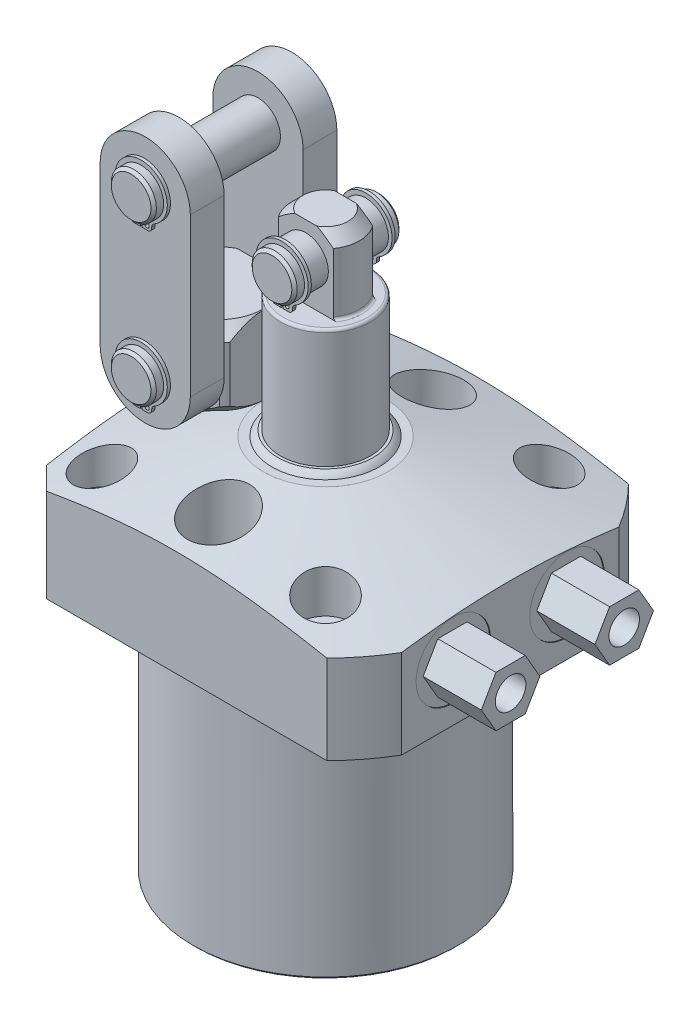
SolidWorks part; units mm, degrees
material "Alloy Steel"
ref_plane "Front Plane" through (0, 0, 0) normal (0, 0, 1) x (1, 0, 0)
ref_plane "Top Plane" through (0, 0, 0) normal (0, 1, 0) x (1, 0, 0)
ref_plane "Right Plane" through (0, 0, 0) normal (1, 0, 0) x (0, 0, -1)
sketch "Sketch28" plane through (0, 0, 0) normal (0, 0, 1) x (1, 0, 0)
  line L0 (0, 0) -> (0, 146.1857) construction
  line L1 (-17.4625, 36.4998) -> (-60.325, 25.0148)
  line L2 (-60.325, 25.0148) -> (-60.325, 0)
  line L3 (-60.325, 0) -> (-37.2999, 0)
  line L6 (-37.2999, 0) -> (-37.2999, -69.85)
  line L9 (-37.2999, -69.85) -> (0, -69.85)
  line L10 (0, -69.85) -> (0, 36.4998)
  line L11 (0, 36.4998) -> (-17.4625, 36.4998)
  dimension "D2" = 74.5998
  dimension "D3" = 69.85
  dimension "D5" = 120.65
  dimension "D6" = 15
  dimension "D7" = 34.925
  dimension "D8" = 36.4998
revolve "Revolve7" add sketch "Sketch28" angle 360 about L0
sketch "Sketch3" plane through (0, 36.4998, 0) normal (0, 1, 0) x (-1, 0, 0)
  line L0 (42.4688, -42.4688) -> (-51.9938, -42.4688)
  line L3 (-51.9938, 42.4688) -> (42.4688, 42.4688)
  line L4 (42.4688, -42.4688) -> (42.4688, 42.4688)
  line L5 (-51.9938, -42.4688) -> (-51.9938, 42.4688)
  line L6 (-29.7523, 0) -> (31.3525, 0) construction
  dimension "D1" = 84.9376
  dimension "D2" = 51.9938
  dimension "D5" = 42.4688
extrude "Cut-Extrude9" cut sketch "Sketch3" against normal up to next (106.3498 mm away) flip side to cut
chamfer "Chamfer8" distance 6.35 angle 45 2 edges at (-42.4688, 12.5429, -42.4688) (-42.4688, 12.5429, 42.4688)
chamfer "Chamfer5" distance 0.762 angle 45 1 edges at (0, -69.85, -37.2999)
hole_wizard "Hole1" positions "Sketch32" profile "Sketch31" legacy
sketch "Sketch32" plane through (0, 36.4998, 0) normal (0, 1, 0) x (-1, 0, 0)
  line L1 (0, 0) -> (-56.2722, 0) construction
  line L2 (0, 0) -> (0, 46.6984) construction
  point P11 (-31.496, -31.496)
  point P23 (-31.496, 31.496)
  point P25 (31.496, -31.496)
  point P26 (31.496, 31.496)
  dimension "D1" = 62.992
  dimension "D2" = 62.992
sketch "Sketch31" plane through (31.496, 36.4998, -31.496) normal (1, 0, 0) x (0, 0, 1)
  line L0 (0, 0) -> (0, 36.4998)
  line L1 (0, 36.4998) -> (4.3688, 36.4998)
  line L2 (4.3688, 36.4998) -> (4.3688, 17.4498)
  line L3 (4.3688, 17.4498) -> (7.1374, 17.4498)
  line L4 (7.1374, 17.4498) -> (7.1374, 0)
  line L5 (7.1374, 0) -> (0, 0)
  line L6 (0, 110) -> (0, -10) construction
  dimension "Diameter" = 8.7376
  dimension "Depth" = 36.4998
  dimension "C-Bore Diameter" = 14.2748
  dimension "C-Bore Depth" = 17.4498
sketch "Sketch34" plane through (0, 36.4998, 0) normal (0, 1, 0) x (1, 0, 0)
  line L0 (0, 0) -> (-28.6526, 0) construction
  circle A0 centre (0, 30.1498) radius 8.7503
  circle A1 centre (0, -30.1498) radius 8.7503
  circle A2 centre (0, 0) radius 30.1498 construction
  circle A3 centre (-30.1498, 0) radius 8.7503
  dimension "D1" = 17.5006
  dimension "D2" = 30.1498
extrude "Cut-Extrude10" cut sketch "Sketch34" against normal blind 19.05
ref_plane "Plane23" through (0, 15.875, 0) normal (0, -1, 0) x (1, 0, 0)
sketch "S2D0007" plane through (0, 15.875, 0) normal (0, -1, 0) x (1, 0, 0)
  line L0 (51.9938, -16.002) -> (51.9938, -26.4795)
  line L1 (51.9938, -26.4795) -> (51.7398, -26.4795)
  line L2 (51.7398, -26.4795) -> (51.7398, -22.2186)
  line L3 (51.7398, -22.2186) -> (49.6697, -21.7786)
  line L4 (49.6697, -21.7786) -> (48.8715, -20.9804)
  line L5 (48.8715, -20.9804) -> (37.7698, -20.9804)
  line L6 (37.7698, -20.9804) -> (34.7785, -16.002)
  line L7 (34.7785, -16.002) -> (51.9938, -16.002)
  line L8 (-11.7468, -16.002) -> (-12.1894, -16.002) construction
  line L10 (51.9938, -30.59) -> (51.9938, 30.59) construction
  dimension "D1" = 12.4333
  dimension "D2" = 59
  dimension "D3" = 9.9568
  dimension "D4" = 45
  dimension "D5" = 12
  dimension "D6" = 2.0701
  dimension "D7" = 0.254
  dimension "D8" = 20.955
  dimension "D9" = 16.002
  dimension "D10" = 13.97
revolve "Cut-Revolve2" cut sketch "S2D0007" angle 360 about L8
ref_plane "Plane24" through (0, 0, -16.002) normal (0, 0, 1) x (1, 0, 0)
sketch "Sketch6" plane through (0, 0, -16.002) normal (0, 0, 1) x (1, 0, 0)
  line L0 (42.8428, 0) -> (-36.1188, 0) construction
  line L1 (50.6793, 0) -> (50.6793, 1.4478)
  line L2 (50.6793, 1.4478) -> (47.6189, 1.4478)
  line L3 (42.8428, 0) -> (51.9938, 0) construction
  line L5 (45.0088, 0.5588) -> (46.1518, 0.5588)
  line L6 (45.0088, 0) -> (50.6793, 0)
  line L8 (45.0088, 0.5588) -> (45.0088, 0)
  line L9 (45.0088, -21.0492) -> (45.0088, 0.6686) construction
  arc A1 (46.1518, 0.5588) -> (47.6189, 1.4478) centre (45.0088, 4.1) ccw
  dimension "D8" = 3.7211
  dimension "D1" = 1.4478
  dimension "D2" = 45.0088
  dimension "D7" = 0.5588
  dimension "D9" = 11.3411
  dimension "D10" = 2.286
revolve "Cut-Revolve3" cut sketch "Sketch6" angle 360 about L9
sketch "Sketch38" plane through (51.7398, 0, 0) normal (1, 0, 0) x (0, 0, -1)
  line L1 (24.2436, 15.875) -> (20.1228, 23.0124)
  line L2 (20.1228, 23.0124) -> (11.8812, 23.0124)
  line L3 (11.8812, 23.0124) -> (7.7604, 15.875)
  line L4 (7.7604, 15.875) -> (11.8812, 8.7376)
  line L5 (11.8812, 8.7376) -> (20.1228, 8.7376)
  line L6 (20.1228, 8.7376) -> (24.2436, 15.875)
  circle A0 centre (16.002, 15.875) radius 7.1374 construction
  dimension "D1" = 14.2748
extrude "Extrude14" add sketch "Sketch38" along normal blind 16.383
hole_wizard "Hole2" positions "Sketch40" profile "Sketch39" legacy
sketch "Sketch40" plane through (68.1228, 0, 0) normal (1, 0, 0) x (0, 0, -1)
  circle A0 centre (16.002, 15.875) radius 10.4775 construction
  point P0 (16.002, 15.875)
sketch "Sketch39" plane through (68.1228, 15.875, -16.002) normal (0, 1, 0) x (0, 0, -1)
  line L0 (0, 0) -> (0, 6.7056)
  line L1 (0, 6.7056) -> (4.3053, 6.7056)
  line L2 (4.3053, 6.7056) -> (4.3053, 0)
  line L3 (4.3053, 0) -> (0, 0)
  line L4 (0, 110) -> (0, -10) construction
  dimension "Diameter" = 8.6106
  dimension "Depth" = 6.7056
mirror "Mirror6" about plane through (0, 0, 0) normal (0, 0, 1) of "Hole2", "Extrude14", "Cut-Revolve2", "Cut-Revolve3"
sketch "Sketch33" plane through (0, 0, -16.002) normal (0, 0, 1) x (1, 0, 0)
  line L0 (45.0088, 8.3297) -> (45.0088, -4.9597) construction
  line L1 (45.0088, 2.4904) -> (45.0088, -1.971) construction
  line L2 (39.3383, 1.4478) -> (50.6793, 1.4478) construction
  circle A0 centre (40.2272, 0.5842) radius 0.889
  dimension "D3" = 1.778
  dimension "D1" = 9.5631
  dimension "D2" = 0.8636
revolve "Revolve9" add sketch "Sketch33" angle 360 about L0
mirror "Mirror7" about plane through (0, 0, 0) normal (0, 0, 1) of bodies 147
sketch "Sketch12" plane through (0, 0, 0) normal (0, 0, -1) x (-1, 0, 0)
  line L0 (0, 36.4998) -> (0, 38.0238)
  line L1 (0, 38.0238) -> (13.462, 38.0238)
  line L2 (0, 36.4998) -> (15.0749, 36.4998)
  line L3 (0, 22.1056) -> (0, 27.6194) construction
  line L4 (17.4625, 36.4998) -> (-17.4625, 36.4998) construction
  arc A0 (15.0749, 36.4998) -> (13.462, 38.0238) centre (11.0966, 33.9049) ccw
  dimension "D1" = 4.7498
  dimension "D2" = 1.524
  dimension "D3" = 26.924
  dimension "D4" = 30.1498
revolve "Revolve2" add sketch "Sketch12" angle 360 about L3
ref_plane "Plane25" through (0, 0, 0) normal (0, 0, 1) x (1, 0, 0)
sketch "Sketch13" plane through (0, 0, 0) normal (0, 0, 1) x (1, 0, 0)
  line L0 (0, 38.0238) -> (0, 92.075)
  line L1 (0, 92.075) -> (6.35, 92.075)
  line L2 (6.35, 92.075) -> (9.525, 88.9)
  line L3 (9.525, 71.4502) -> (9.525, 88.9)
  line L4 (12.6937, 38.0238) -> (0, 38.0238)
  line L5 (0, 23.0264) -> (0, 64.961) construction
  line L6 (-6.0362, 82.55) -> (17.7755, 82.55) construction
  line L7 (13.462, 38.0238) -> (-13.462, 38.0238) construction
  line L8 (42.8428, 0) -> (-36.1188, 0) construction
  line L10 (9.525, 71.4502) -> (12.6937, 71.4502)
  line L11 (12.6937, 71.4502) -> (12.6937, 38.0238)
  dimension "D1" = 9.525
  dimension "D2" = 82.55
  dimension "D3" = 19.05
  dimension "D4" = 45
  dimension "D5" = 3.175
  dimension "D6" = 25.3873
  dimension "D7" = 20.6248
revolve "Revolve3" add sketch "Sketch13" angle 360 about L5
sketch "Sketch14" plane through (0, 92.075, 0) normal (0, 1, 0) x (-1, 0, 0)
  line L0 (-7.7411, 5.5499) -> (7.7411, 5.5499)
  line L2 (7.7411, -5.5499) -> (-7.7411, -5.5499)
  line L4 (0, 0) -> (-0.0001, 0) construction
  line L5 (34.2265, 0) -> (-34.2265, 0) construction
  circle A0 centre (0, 0) radius 9.525 construction
  arc A1 (7.7411, 5.5499) -> (-7.7411, 5.5499) centre (0, 0) ccw
  arc A2 (-7.7411, -5.5499) -> (7.7411, -5.5499) centre (0, 0) ccw
  dimension "D1" = 11.0998
extrude "Cut-Extrude7" cut sketch "Sketch14" against normal up to surface (20.6248 mm away) up to face at (0, 71.4502, -9.525)
fillet "Fillet4" radius 0.762 3 edges at (0, 71.4502, -12.6937) (-9.525, 71.4502, 0) (9.525, 71.4502, 0)
sketch "Sketch29" plane through (0, 0, 0) normal (0, 0, 1) x (1, 0, 0)
  line L0 (-3.0856, 92.075) -> (-6.35, 92.075) construction
  circle A0 centre (0, 82.55) radius 6.3373
  dimension "D1" = 12.6746
  dimension "D2" = 9.525
extrude "Extrude11" add sketch "Sketch29" along normal mid plane 30.1498
sketch "Sketch16" plane through (0, 52.3748, 15.0749) normal (0, 0, 1) x (1, 0, 0)
  line L0 (0.2388, 24.2364) -> (0.2388, 21.4932)
  line L1 (2.982, 22.9316) -> (2.982, 22.687)
  line L2 (1.7882, 21.4932) -> (0.2388, 21.4932)
  line L3 (-2.982, 22.9316) -> (-2.982, 22.687)
  line L4 (-1.7882, 21.4932) -> (-0.2388, 21.4932)
  line L5 (-0.2388, 24.2364) -> (-0.2388, 21.4932)
  line L6 (0, -3.8062) -> (0, 3.1748) construction
  arc A0 (0.2388, 24.2364) -> (-0.2388, 24.2364) centre (0, 30.1752) ccw
  arc A1 (3.5934, 23.9737) -> (-3.5934, 23.9737) centre (0, 30.4038) ccw
  arc A2 (3.5934, 23.9737) -> (2.982, 22.9316) centre (4.1758, 22.9316) ccw
  arc A3 (1.7882, 21.4932) -> (2.982, 22.687) centre (1.7882, 22.687) ccw
  circle A4 centre (1.4326, 22.687) radius 0.5969
  arc A5 (-3.5934, 23.9737) -> (-2.982, 22.9316) centre (-4.1758, 22.9316) cw
  arc A6 (-1.7882, 21.4932) -> (-2.982, 22.687) centre (-1.7882, 22.687) cw
  circle A7 centre (-1.4326, 22.687) radius 0.5969
  circle A8 centre (0, 30.1752) radius 6.3373 construction
  dimension "D1" = 7.366
  dimension "D4" = 1.1938
  dimension "D6" = 1.1938
  dimension "D7" = 2.7432
  dimension "D8" = 5.9436
  dimension "D10" = 1.1938
  dimension "D11" = 1.1938
  dimension "D2" = 2.7432
  dimension "D3" = 0.2286
  dimension "D5" = 1.4326
  dimension "D9" = 0.4775
extrude "Extrude2" add sketch "Sketch16" against normal blind 0.889 from offset 2.8194
chamfer "Chamfer6" distance 0.762 angle 45 2 edges at (6.3373, 82.55, -15.0749) (6.3373, 82.55, 15.0749)
mirror "Mirror2" about plane through (0, 0, 0) normal (0, 0, 1) of "Extrude2"
sketch "Sketch35" plane through (0, 0, 0) normal (0, 0, 1) x (1, 0, 0)
  line L0 (-30.1498, 43.5741) -> (-30.1498, 11.6793) construction
  line L1 (-30.1498, 17.4498) -> (-20.6248, 17.4498)
  line L2 (-20.6248, 17.4498) -> (-20.6248, 36.4998)
  line L3 (-20.6248, 36.4998) -> (-17.5768, 36.4998)
  line L4 (-14.2748, 39.8018) -> (-14.2748, 55.4228)
  line L5 (-17.5768, 58.7248) -> (-30.1498, 58.7248)
  line L6 (-30.1498, 58.7248) -> (-30.1498, 17.4498)
  line L8 (-14.2748, 55.4228) -> (-17.5768, 58.7248)
  line L9 (-17.5768, 36.4998) -> (-14.2748, 39.8018)
  line L10 (42.8428, 0) -> (51.9938, 0) construction
  point P6 (-14.2748, 36.4998)
  point P7 (-14.2748, 58.7248)
  dimension "D2" = 19.05
  dimension "D3" = 31.75
  dimension "D4" = 41.275
  dimension "D5" = 22.225
  dimension "D6" = 30.1498
  dimension "D9" = 3.302
  dimension "D10" = 3.302
  dimension "D7" = 36.4998
revolve "Revolve10" add sketch "Sketch35" angle 360 about L0
sketch "Sketch36" plane through (0, 58.7248, 0) normal (0, 1, 0) x (1, 0, 0)
  line L0 (-30.1498, 0) -> (-30.1498, 48.7489) construction
  line L1 (-41.4868, 11.1125) -> (-18.8128, 11.1125)
  line L2 (-42.8498, 9.525) -> (-42.8498, -9.525)
  line L3 (-41.4868, -11.1125) -> (-18.8128, -11.1125)
  line L4 (-17.4498, 9.525) -> (-17.4498, -9.525)
  line L5 (-30.1498, 0) -> (0, 0) construction
  line L6 (-34.2265, 0) -> (34.2265, 0) construction
  circle A0 centre (-30.1498, 0) radius 15.875 construction
  arc A2 (-42.8498, 9.525) -> (-42.8498, -9.525) centre (-30.1498, 0) ccw
  arc A3 (-41.4868, -11.1125) -> (-18.8128, -11.1125) centre (-30.1498, 0) ccw
  arc A4 (-18.8128, 11.1125) -> (-41.4868, 11.1125) centre (-30.1498, 0) ccw
  arc A5 (-17.4498, -9.525) -> (-17.4498, 9.525) centre (-30.1498, 0) ccw
  dimension "D1" = 25.4
  dimension "D2" = 22.225
extrude "Cut-Extrude11" cut sketch "Sketch36" against normal up to surface (22.225 mm away) up to face at (-42.7228, 36.4998, 0)
sketch "Sketch30" plane through (0, 0, 0) normal (0, 0, 1) x (1, 0, 0)
  line L0 (-60.325, 0) -> (-42.8428, 0) construction
  circle A0 centre (-30.1498, 47.625) radius 6.3373
  dimension "D3" = 12.6746
  dimension "D1" = 47.625
  dimension "D2" = 30.1498
extrude "Extrude12" add sketch "Sketch30" along normal mid plane 49.1998
sketch "Sketch19" plane through (-22.225, 11.0998, 24.5999) normal (0, 0, 1) x (1, 0, 0)
  line L0 (-7.686, 30.5864) -> (-7.686, 27.8432)
  line L1 (-4.9428, 29.2816) -> (-4.9428, 29.037)
  line L2 (-6.1366, 27.8432) -> (-7.686, 27.8432)
  line L3 (-10.9068, 29.2816) -> (-10.9068, 29.037)
  line L4 (-9.713, 27.8432) -> (-8.1636, 27.8432)
  line L5 (-8.1636, 30.5864) -> (-8.1636, 27.8432)
  line L6 (-7.9248, -5.3833) -> (-7.9248, 4.2478) construction
  arc A0 (-7.686, 30.5864) -> (-8.1636, 30.5864) centre (-7.9248, 36.5252) ccw
  arc A1 (-4.3314, 30.3237) -> (-11.5182, 30.3237) centre (-7.9248, 36.7538) ccw
  arc A2 (-4.3314, 30.3237) -> (-4.9428, 29.2816) centre (-3.749, 29.2816) ccw
  arc A3 (-6.1366, 27.8432) -> (-4.9428, 29.037) centre (-6.1366, 29.037) ccw
  circle A4 centre (-6.2535, 29.037) radius 0.5969
  arc A5 (-11.5182, 30.3237) -> (-10.9068, 29.2816) centre (-12.1006, 29.2816) cw
  arc A6 (-9.713, 27.8432) -> (-10.9068, 29.037) centre (-9.713, 29.037) cw
  circle A7 centre (-9.5961, 29.037) radius 0.5969
  circle A8 centre (-7.9248, 36.5252) radius 6.3373 construction
  dimension "D1" = 7.366
  dimension "D3" = 0.2286
  dimension "D4" = 1.1938
  dimension "D5" = 1.1938
  dimension "D6" = 1.1938
  dimension "D9" = 5.9436
  dimension "D2" = 2.7432
  dimension "D7" = 0.4775
  dimension "D8" = 2.7432
  dimension "D10" = 1.1938
  dimension "D11" = 1.4326
extrude "Extrude4" add sketch "Sketch19" against normal blind 0.889 from offset 2.8194
sketch "Sketch37" plane through (0, 0, 11.1125) normal (0, 0, 1) x (1, 0, 0)
  line L0 (-42.8498, 92.075) -> (-42.8498, 47.625)
  line L1 (-17.4498, 92.075) -> (-17.4498, 47.625)
  arc A0 (-17.4498, 92.075) -> (-42.8498, 92.075) centre (-30.1498, 92.075) ccw
  arc A1 (-42.8498, 47.625) -> (-17.4498, 47.625) centre (-30.1498, 47.625) ccw
  dimension "D1" = 25.4
  dimension "D2" = 44.45
  dimension "D3" = 31.6186
extrude "Extrude13" add sketch "Sketch37" along normal blind 9.525
mirror "Mirror3" about plane through (0, 0, 0) normal (0, 0, 1) of "Extrude4"
chamfer "Chamfer7" distance 0.762 angle 45 2 edges at (-23.8125, 47.625, -24.5999) (-23.8125, 47.625, 24.5999)
pattern_linear "LPattern2" count 2 spacing 44.45 along (0, 1, 0) of "Extrude4", "Mirror3", "Chamfer7", "Extrude12"
mirror "Mirror8" about plane through (0, 0, 0) normal (0, 0, 1) of "Extrude13"
